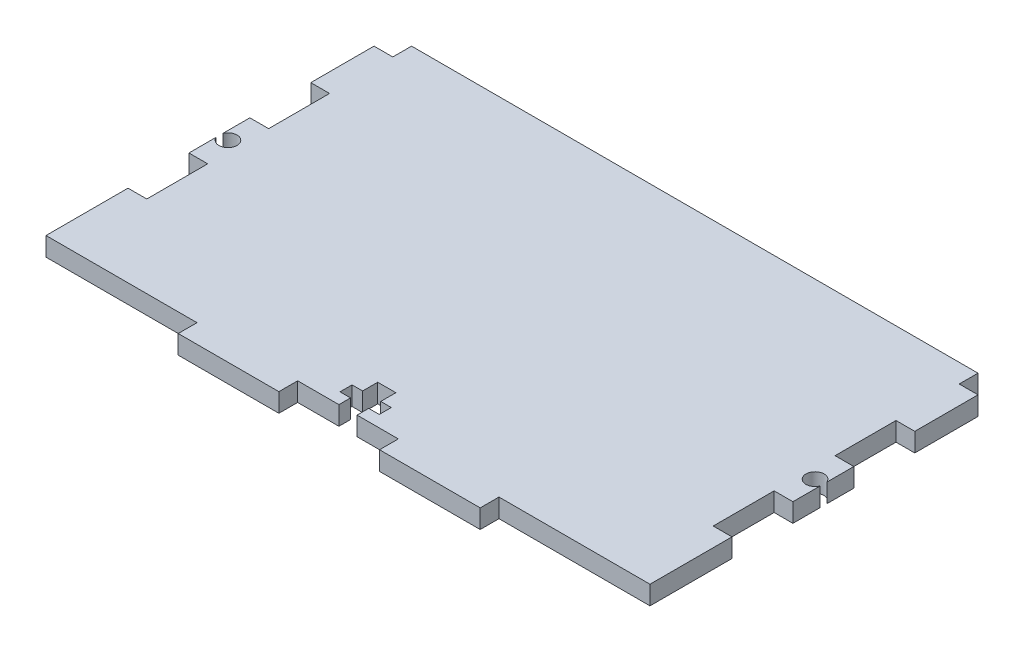
SolidWorks part; units mm, degrees
ref_plane "Front Plane" through (0, 0, 0) normal (0, 0, 1) x (1, 0, 0)
ref_plane "Top Plane" through (0, 0, 0) normal (0, 1, 0) x (1, 0, 0)
ref_plane "Right Plane" through (0, 0, 0) normal (1, 0, 0) x (0, 0, -1)
sketch "Sketch2" plane through (0, 0, 0) normal (0, 1, 0) x (1, 0, 0)
  line L1 (-48.26, 27.71) -> (48.26, 27.71)
  line L2 (-48.26, 27.71) -> (-48.26, -27.71)
  line L3 (-48.26, -27.71) -> (48.26, -27.71)
  line L4 (48.26, 27.71) -> (48.26, -27.71)
  line L5 (-48.26, 27.71) -> (48.26, -27.71) construction
  line L6 (-48.26, -27.71) -> (48.26, 27.71) construction
  point P0 (0, 0)
  dimension "D1" = 96.52
  dimension "D2" = 55.42
extrude "Boss-Extrude1" add sketch "Sketch2" along normal blind 3
sketch "Sketch3" plane through (-48.26, 0, 0) normal (-1, 0, 0) x (0, 0, 1)
  line L5 (-27.71, 3) -> (27.71, 3) construction
  line L6 (-27.71, 0) -> (27.71, 0) construction
  line L11 (-14.605, 3) -> (14.605, 3)
  line L12 (-14.605, 3) -> (-14.605, 0)
  line L13 (-14.605, 0) -> (14.605, 0)
  line L14 (14.605, 3) -> (14.605, 0)
  point P4 (0, 0)
  point P5 (0, 0)
  dimension "D1" = 29.21
extrude "Cut-Extrude1" cut sketch "Sketch3" against normal blind 3
mirror "Mirror1" about plane through (0, 0, 0) normal (1, 0, 0) of "Cut-Extrude1"
sketch "Sketch5" plane through (0, 0, 27.71) normal (0, 0, 1) x (1, 0, 0)
  line L5 (-48.26, 3) -> (48.26, 3) construction
  line L11 (-24.13, 3) -> (24.13, 3)
  line L12 (-24.13, 3) -> (-24.13, 0)
  line L13 (-24.13, 0) -> (24.13, 0)
  line L14 (24.13, 3) -> (24.13, 0)
  point P0 (0, 0)
  dimension "D1" = 48.26
extrude "Boss-Extrude2" add sketch "Sketch5" along normal blind 3
sketch "Sketch14" plane through (0, 0, 30.71) normal (0, 0, 1) x (1, 0, 0)
  line L0 (24.13, 3) -> (-24.13, 3) construction
  line L1 (8.0433, 3) -> (-8.0433, 3)
  line L2 (8.0433, 3) -> (8.0433, 0)
  line L3 (8.0433, 0) -> (-8.0433, 0)
  line L4 (-8.0433, 3) -> (-8.0433, 0)
  line L5 (-24.13, 0) -> (24.13, 0) construction
  point P6 (0, 0)
  point P9 (0, 0)
  dimension "D1" = 16.0867
extrude "Cut-Extrude2" cut sketch "Sketch14" against normal blind 3
sketch "Sketch15" plane through (45.26, 0, 0) normal (1, 0, 0) x (0, 0, -1)
  line L0 (14.605, 0) -> (-14.605, 0) construction
  line L1 (-4.869, 0) -> (4.869, 0)
  line L2 (-4.869, 0) -> (-4.869, 3)
  line L3 (-4.869, 3) -> (4.869, 3)
  line L4 (4.869, 0) -> (4.869, 3)
  line L5 (-14.605, 3) -> (14.605, 3) construction
  point P6 (0, 3)
  point P9 (0, 3)
  dimension "D1" = 9.7379
extrude "Boss-Extrude9" add sketch "Sketch15" along normal blind 3
mirror "Mirror2" about plane through (0, 0, 0) normal (1, 0, 0) of "Boss-Extrude9"
sketch "Sketch26" plane through (0, 0, -27.71) normal (0, 0, -1) x (-1, 0, 0)
  line L0 (-48.26, 0) -> (48.26, 0) construction
  line L1 (-48.26, 3) -> (-45.26, 3)
  line L2 (-48.26, 3) -> (-48.26, 0)
  line L3 (-48.26, 0) -> (-45.26, 0)
  line L4 (-45.26, 3) -> (-45.26, 0)
  dimension "D1" = 3
extrude "Cut-Extrude4" cut sketch "Sketch26" against normal blind 3
mirror "Mirror3" about plane through (0, 0, 0) normal (1, 0, 0) of "Cut-Extrude4"
sketch "Sketch27" plane through (0, 0, 0) normal (0, -1, 0) x (1, 0, 0)
  line L0 (48.26, 4.869) -> (48.26, -4.869) construction
  line L1 (48.36, 1.4825) -> (45.36, 1.4825)
  line L2 (48.36, 1.4825) -> (48.36, -1.5175)
  line L3 (48.36, -1.5175) -> (45.36, -1.5175)
  line L4 (45.36, 1.4825) -> (45.36, -1.5175)
  circle A0 centre (46.91, -0.0175) radius 1.45
  point P5 (0, 0)
  line M14 (48.26, -4.869) -> (48.26, 4.869)
  dimension "D3" = 2.9
  dimension "D1" = 3
  dimension "D2" = 3
  dimension "D4" = 0.1
extrude "Cut-Extrude5" cut sketch "Sketch27" against normal blind 3 contours A0 M14
mirror "Mirror4" about plane through (0, 0, 0) normal (1, 0, 0) of "Cut-Extrude5"
sketch "Sketch29" plane through (0, 0, 27.71) normal (0, 0, 1) x (1, 0, 0)
  line L0 (-8.0433, 0) -> (8.0433, 0) construction
  line L1 (1.45, 3) -> (-1.45, 3)
  line L2 (1.45, 3) -> (1.45, 0)
  line L3 (1.45, 0) -> (-1.45, 0)
  line L4 (-1.45, 3) -> (-1.45, 0)
  line L6 (8.0433, 3) -> (-8.0433, 3) construction
  point P4 (0, 0)
  point P7 (0, 0)
  dimension "D1" = 2.9
extrude "Cut-Extrude6" cut sketch "Sketch29" against normal blind 6.2
sketch "Sketch30" plane through (0, 0, 0) normal (0, -1, 0) x (1, 0, 0)
  line L0 (-1.45, 21.51) -> (1.45, 21.51) construction
  line L1 (-3.135, 25.8521) -> (3.135, 25.8521)
  line L2 (-3.135, 25.8521) -> (-3.135, 23.9256)
  line L3 (-3.135, 23.9256) -> (3.135, 23.9256)
  line L4 (3.135, 25.8521) -> (3.135, 23.9256)
  point P4 (0, 23.9256)
  point P7 (0, 21.51)
  dimension "D1" = 6.27
extrude "Cut-Extrude7" cut sketch "Sketch30" against normal blind 3 contours L2 L1 L4 L3
